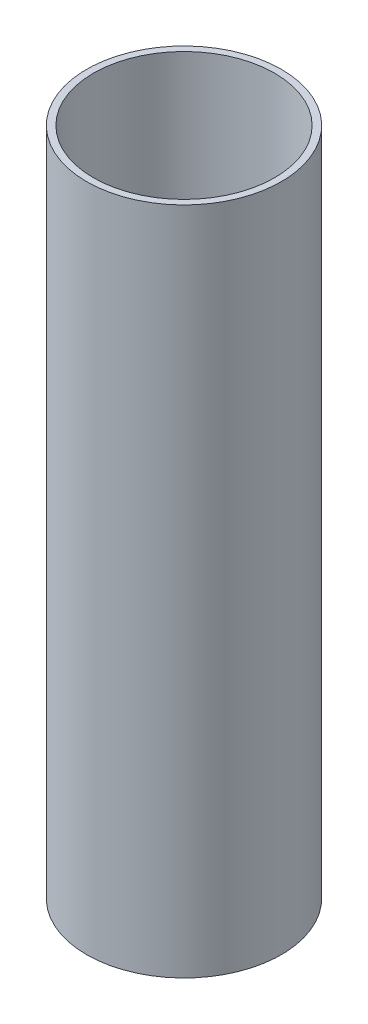
SolidWorks part; units mm, degrees
ref_plane "Front Plane" through (0, 0, 0) normal (0, 0, 1) x (1, 0, 0)
ref_plane "Top Plane" through (0, 0, 0) normal (0, 1, 0) x (1, 0, 0)
ref_plane "Right Plane" through (0, 0, 0) normal (1, 0, 0) x (0, 0, -1)
sketch "Sketch1" plane through (0, 0, 0) normal (0, 1, 0) x (1, 0, 0)
  circle A0 centre (0, 0) radius 27.0675
  circle A1 centre (0, 0) radius 29.083
  dimension "D1" = 54.135
  dimension "D2" = 58.166
extrude "Boss-Extrude1" add sketch "Sketch1" along normal blind 200
